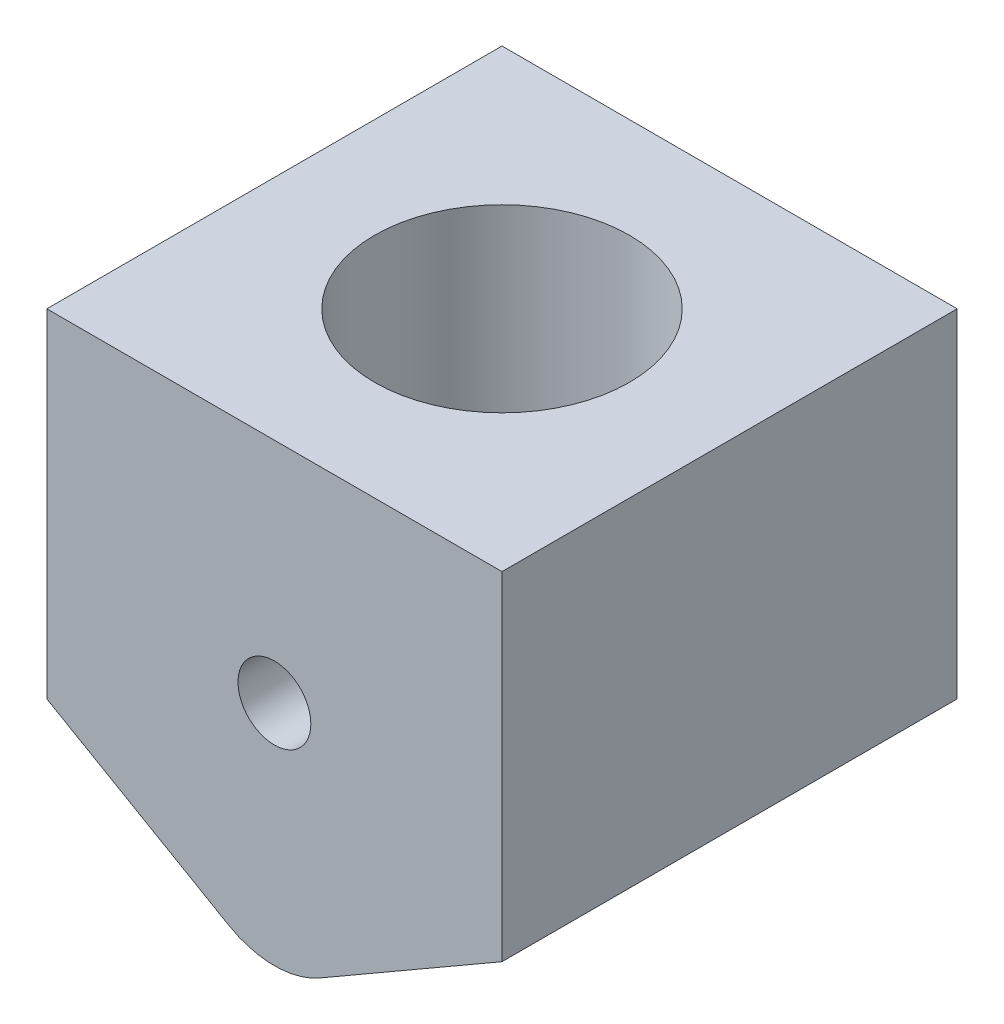
SolidWorks part; units mm, degrees
material "1.0050 (E295)"
ref_plane "Front Plane" through (0, 0, 0) normal (0, 0, 1) x (1, 0, 0)
ref_plane "Top Plane" through (0, 0, 0) normal (0, 1, 0) x (1, 0, 0)
ref_plane "Right Plane" through (0, 0, 0) normal (1, 0, 0) x (0, 0, -1)
sketch "Sketch1" plane through (0, 0, 0) normal (0, 0, 1) x (1, 0, 0)
  line L0 (0, 35.3553) -> (0, -59.9851) construction
  line L1 (-25, 0) -> (25, 0)
  line L2 (25, 0) -> (25, -37.1132)
  line L3 (25, -37.1132) -> (5, -48.6603)
  line L4 (-25, -37.1132) -> (-5, -48.6603)
  line L5 (-25, 0) -> (-25, -37.1132)
  arc A0 (5, -48.6603) -> (-5, -48.6603) centre (0, -40) cw
  point P8 (0, -50)
  point P14 (0, 0)
  dimension "D3" = 10
  dimension "D1" = 50
  dimension "D2" = 60
  dimension "D4" = 50
extrude "Boss-Extrude1" add sketch "Sketch1" along normal mid plane 50
sketch "Sketch2" plane through (0, 0, 0) normal (0, 1, 0) x (1, 0, 0)
  circle A0 centre (0, 0) radius 14
  dimension "D1" = 28
extrude "Cut-Extrude1" cut sketch "Sketch2" against normal blind 29
sketch "Sketch3" plane through (0, 0, 25) normal (0, 0, 1) x (1, 0, 0)
  line L0 (14, -29) -> (-14, -29) construction
  circle A0 centre (0, -25) radius 4
  dimension "D1" = 8
extrude "Cut-Extrude2" cut sketch "Sketch3" against normal up to next
cosmetic thread "Cosmetic Thread1" parameters "D2"=10
